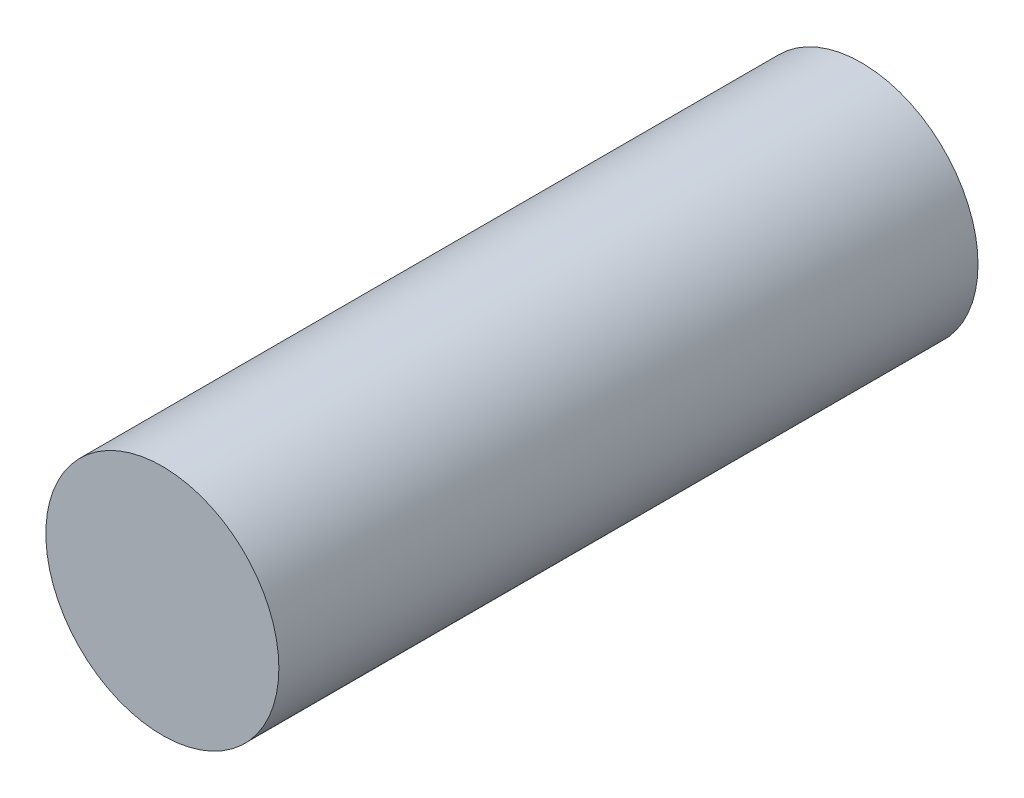
SolidWorks part; units mm, degrees
material "PLA"
ref_plane "Front Plane" through (0, 0, 0) normal (0, 0, 1) x (1, 0, 0)
ref_plane "Top Plane" through (0, 0, 0) normal (0, 1, 0) x (1, 0, 0)
ref_plane "Right Plane" through (0, 0, 0) normal (1, 0, 0) x (0, 0, -1)
sketch "Sketch1" plane through (0, 0, 0) normal (0, 0, 1) x (1, 0, 0)
  circle A0 centre (0, 0) radius 2.5
extrude "Boss-Extrude1" add sketch "Sketch1" along normal mid plane 15
